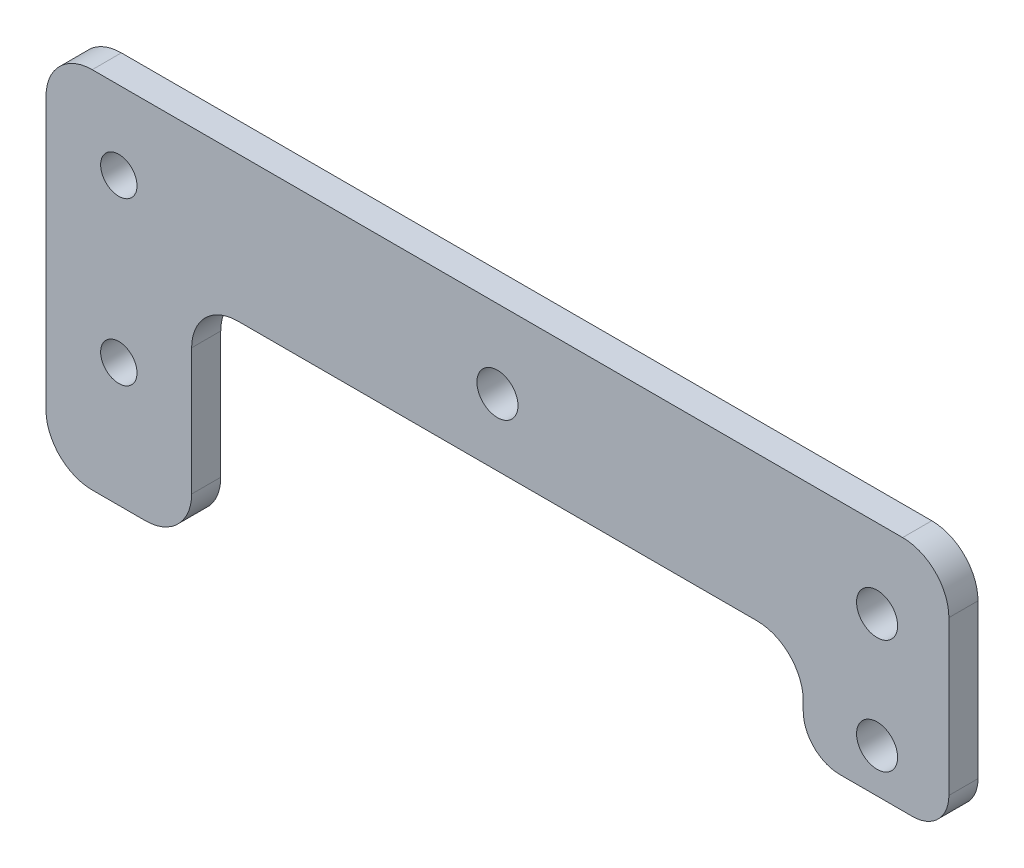
SolidWorks part; units mm, degrees
ref_plane "Alzado" through (0, 0, 0) normal (0, 0, 1) x (1, 0, 0)
ref_plane "Planta" through (0, 0, 0) normal (0, 1, 0) x (1, 0, 0)
ref_plane "Vista lateral" through (0, 0, 0) normal (1, 0, 0) x (0, 0, -1)
sketch "Croquis1" plane through (0, 0, 0) normal (0, 0, 1) x (1, 0, 0)
  line L1 (26.3934, 6.6994) -> (97.6934, 6.6994)
  line L2 (0.0434, 6.6044) -> (0.0434, 20.2544)
  line L3 (6.3934, 26.6044) -> (117.6934, 26.6044)
  line L4 (124.0434, 6.6044) -> (124.0434, 20.2544)
  line L6 (0.0434, 6.6044) -> (0.0434, -17.0456)
  line L7 (6.3934, -23.3956) -> (13.6934, -23.3956)
  line L8 (20.0434, 0.3494) -> (20.0434, -17.0456)
  line L13 (62.0434, 26.6044) -> (62.0434, -35.7819) construction
  line L14 (124.0434, 6.6044) -> (124.0434, -0.8956)
  line L15 (119.0434, -5.8956) -> (109.0434, -5.8956)
  line L16 (104.0434, -0.8956) -> (104.0434, 0.3494)
  circle A1 centre (10.0434, 15.8665) radius 2.5
  circle A2 centre (114.1834, 15.7714) radius 2.8214
  circle A3 centre (10.0434, -6.3956) radius 2.5
  arc A5 (26.3934, 6.6994) -> (20.0434, 0.3494) centre (26.3934, 0.3494) ccw
  arc A6 (124.0434, 20.2544) -> (117.6934, 26.6044) centre (117.6934, 20.2544) ccw
  arc A7 (6.3934, 26.6044) -> (0.0434, 20.2544) centre (6.3934, 20.2544) ccw
  arc A8 (104.0434, 0.3494) -> (97.6934, 6.6994) centre (97.6934, 0.3494) ccw
  arc A9 (6.3934, -23.3956) -> (0.0434, -17.0456) centre (6.3934, -17.0456) cw
  arc A10 (13.6934, -23.3956) -> (20.0434, -17.0456) centre (13.6934, -17.0456) ccw
  circle A24 centre (62.0434, 15.8665) radius 2.8214
  circle A33 centre (114.1834, 0.1044) radius 2.8214
  arc A34 (119.0434, -5.8956) -> (124.0434, -0.8956) centre (119.0434, -0.8956) ccw
  arc A35 (109.0434, -5.8956) -> (104.0434, -0.8956) centre (109.0434, -0.8956) cw
  point P22 (20.0434, 6.6994)
  point P25 (124.0434, 26.6044)
  point P28 (0.0434, 26.6044)
  point P31 (114.1981, 6.6994)
  point P34 (0.0434, -23.3956)
  point P37 (20.0434, -23.3956)
  dimension "D8" = 5
  dimension "D10" = 5
  dimension "D11" = 9.86
  dimension "D19" = 6.35
  dimension "D20" = 6.35
  dimension "D21" = 6.35
  dimension "D5" = 26.5
  dimension "D1" = 20
  dimension "D2" = 124
  dimension "D3" = 30
  dimension "D4" = 20
  dimension "D6" = 6
  dimension "D15" = 10
  dimension "D16" = 10
  dimension "D18" = 94.1547
extrude "Saliente-Extruir1" add sketch "Croquis1" along normal blind 4
